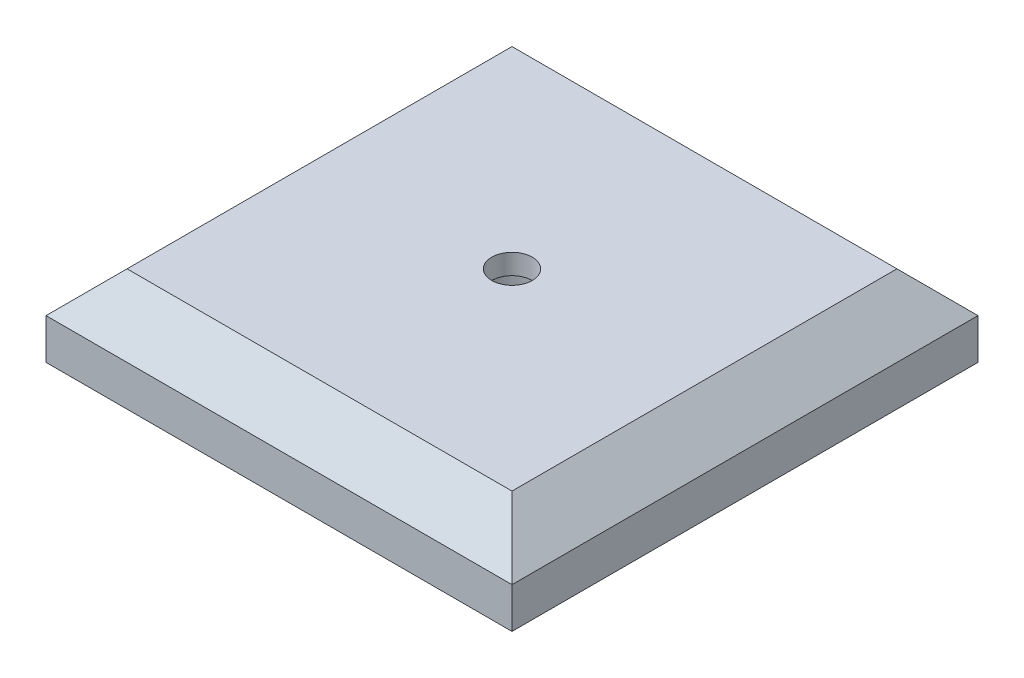
SolidWorks part; units mm, degrees
ref_plane "Front Plane" through (0, 0, 0) normal (0, 0, 1) x (1, 0, 0)
ref_plane "Top Plane" through (0, 0, 0) normal (0, 1, 0) x (1, 0, 0)
ref_plane "Right Plane" through (0, 0, 0) normal (1, 0, 0) x (0, 0, -1)
sketch "Sketch2" plane through (0, 0, 0) normal (0, 1, 0) x (1, 0, 0)
  line L1 (-14.375, -14.375) -> (14.375, -14.375)
  line L2 (-14.375, -14.375) -> (-14.375, 14.375)
  line L3 (-14.375, 14.375) -> (14.375, 14.375)
  line L4 (14.375, -14.375) -> (14.375, 14.375)
  line L5 (-14.375, -14.375) -> (14.375, 14.375) construction
  line L6 (-14.375, 14.375) -> (14.375, -14.375) construction
  point P0 (0, 0)
  dimension "D1" = 28.75
extrude "Boss-Extrude1" add sketch "Sketch2" along normal blind 5
chamfer "Chamfer1" distance 2.5 4 edges at (0, 5, 14.375) (-14.375, 5, 0) (0, 5, -14.375) (14.375, 5, 0)
sketch "Sketch3" plane through (0, 5, 0) normal (0, 1, 0) x (1, 0, 0)
  circle A0 centre (0, 0) radius 1.25
  dimension "D1" = 2.5
extrude "Cut-Extrude1" cut sketch "Sketch3" against normal blind 1.25
ref_plane "Plane1" through (0, 3.75, 0) normal (0, 1, 0) x (1, 0, 0)
sketch "Sketch6" plane through (0, 3.75, 0) normal (0, 1, 0) x (1, 0, 0)
  circle A0 centre (0, 0) radius 2.5
  dimension "D1" = 5
extrude "Cut-Extrude2" cut sketch "Sketch6" against normal blind 3.75
